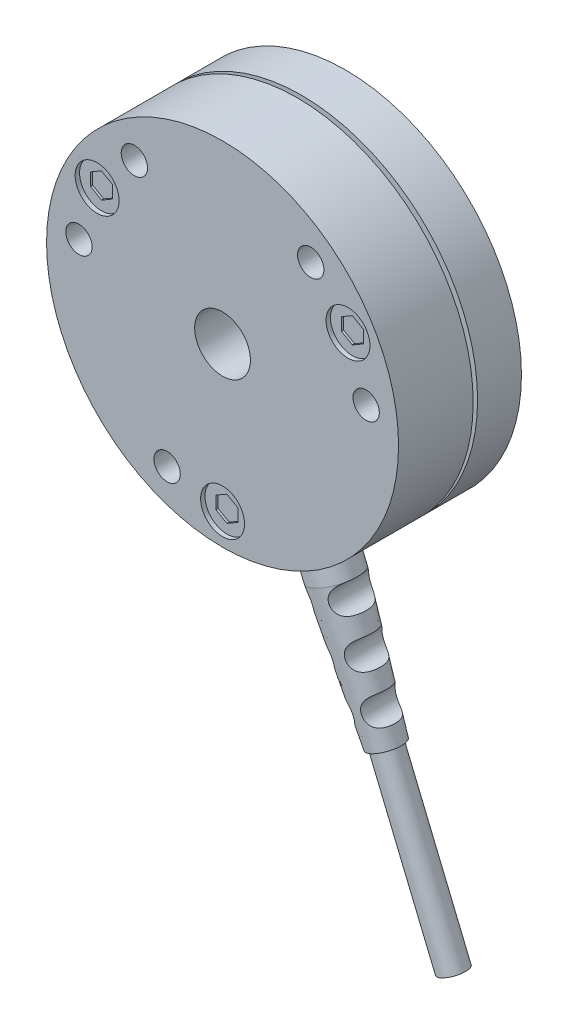
SolidWorks part; units mm, degrees
other "Camera1"
material "Plain Carbon Steel"
ref_plane "Front Plane" through (0, 0, 0) normal (0, 0, 1) x (1, 0, 0)
ref_plane "Top Plane" through (0, 0, 0) normal (0, 1, 0) x (1, 0, 0)
ref_plane "Right Plane" through (0, 0, 0) normal (1, 0, 0) x (0, 0, -1)
sketch "Sketch1" plane through (0, 0, 0) normal (0, 0, 1) x (1, 0, 0)
  circle A0 centre (0, 0) radius 20.05
  dimension "D1" = 40.1
extrude "Boss-Extrude1" add sketch "Sketch1" along normal blind 5
sketch "Sketch2" plane through (0, 0, 5) normal (0, 0, 1) x (1, 0, 0)
  circle A0 centre (0, 0) radius 18.5
  dimension "D1" = 37
extrude "Boss-Extrude2" add sketch "Sketch2" along normal blind 0.5
sketch "Sketch3" plane through (0, 0, 5.5) normal (0, 0, 1) x (1, 0, 0)
  circle A0 centre (0, 0) radius 20.05
extrude "Boss-Extrude3" add sketch "Sketch3" along normal blind 8.5
sketch "Sketch7" plane through (0, 0, 14) normal (0, 0, 1) x (1, 0, 0)
  line L0 (0, 0) -> (7.6728, -18.5238) construction
  line L1 (0, 20.05) -> (0, -20.05) construction
  line L2 (-18.5238, -7.6728) -> (18.5238, 7.6728)
  circle A0 centre (0, 0) radius 20.05 construction
  dimension "D1" = 22.5
sketch "Sketch8" plane through (0, 0, 0) normal (0, 0, -1) x (-1, 0, 0)
  line L0 (-18.5238, 7.6728) -> (18.5238, -7.6728)
  point P3 (0, 0)
ref_plane "Plane4" through (0, 0, 0) normal (-0.3827, 0.9239, 0) x (0.9239, 0.3827, 0)
sketch "Sketch4" plane through (0, 0, 0) normal (-0.3827, 0.9239, 0) x (0.9239, 0.3827, 0)
  line L0 (0, 0) -> (0, -14) construction
  line L1 (-20.05, -14) -> (20.05, -14) construction
  line L2 (-20.05, -7) -> (20.05, -7) construction
  line L3 (-20.05, -5.5) -> (-20.05, -14) construction
  line L4 (20.05, -14) -> (20.05, -5.5) construction
  circle A0 centre (0, -9.65) radius 2.65
  dimension "D1" = 5.3
  dimension "D2" = 7
extrude "Boss-Extrude4" add sketch "Sketch4" against normal blind 37.35 contours A0
chamfer "Chamfer1" distance 15 angle 3 1 edges at (11.8449, -35.521, 9.65)
sketch "Sketch5" plane through (14.2932, -34.5069, 0) normal (0.3827, -0.9239, 0) x (-0.9239, -0.3827, 0)
  circle A0 centre (0, -9.65) radius 1.5
  dimension "D1" = 3
extrude "Boss-Extrude5" add sketch "Sketch5" along normal blind 20
sketch "Sketch6" plane through (0, 0, 0) normal (0, 0, 1) x (1, 0, 0)
  line L0 (11.0013, -19.6346) -> (16.0152, -33.7936) construction
  line L1 (16.0152, -33.7936) -> (18.3361, -40.3477) construction
  line L2 (23.3327, -52.4105) -> (15.679, -33.9329) construction
  line L3 (6.1047, -21.6628) -> (12.5712, -35.2202) construction
  line L4 (12.5712, -35.2202) -> (15.5645, -41.4957) construction
  line L5 (12.9074, -35.0809) -> (20.5611, -53.5585) construction
  line L6 (-921.5262, -418.3454) -> (45272.4504, 18715.8262) construction
  line L7 (-922.1361, -413.1861) -> (45271.8405, 18720.9855) construction
  line L8 (6.1047, -21.6628) -> (11.0013, -19.6346) construction
  circle A0 centre (11.502, -21.0486) radius 1.5
  circle A1 centre (13.1733, -25.7682) radius 1.5
  circle A2 centre (14.8446, -30.4879) radius 1.5
  circle A3 centre (11.0615, -32.0549) radius 1.5
  circle A4 centre (8.906, -27.5358) radius 1.5
  circle A5 centre (6.7505, -23.0167) radius 1.5
  dimension "D1" = 3
  dimension "D2" = 5
  dimension "D3" = 5
extrude "Cut-Extrude1" cut sketch "Sketch6" along normal through all
sketch "Sketch9" plane through (0, 0, 14) normal (0, 0, 1) x (1, 0, 0)
  circle A0 centre (0, 0) radius 16.5 construction
  circle A1 centre (0, -16.5) radius 2.5
  circle A2 centre (-14.2894, 8.25) radius 2.5
  circle A3 centre (14.2894, 8.25) radius 2.5
  dimension "D1" = 33
  dimension "D2" = 5
  dimension "D3" = 3
extrude "Cut-Extrude2" cut sketch "Sketch9" against normal blind 0.5
sketch "Sketch10" plane through (0, 0, 13.5) normal (0, 0, 1) x (1, 0, 0)
  line L0 (-15.5394, 8.9717) -> (-15.5394, 7.5283)
  line L1 (0, -17.9434) -> (1.25, -17.2217)
  line L2 (1.25, -17.2217) -> (1.25, -15.7783)
  line L3 (1.25, -15.7783) -> (0, -15.0566)
  line L4 (0, -15.0566) -> (-1.25, -15.7783)
  line L5 (-1.25, -15.7783) -> (-1.25, -17.2217)
  line L6 (-1.25, -17.2217) -> (0, -17.9434)
  line L7 (-15.5394, 7.5283) -> (-14.2894, 6.8066)
  line L8 (-14.2894, 6.8066) -> (-13.0394, 7.5283)
  line L9 (-13.0394, 7.5283) -> (-13.0394, 8.9717)
  line L10 (-13.0394, 8.9717) -> (-14.2894, 9.6934)
  line L11 (-14.2894, 9.6934) -> (-15.5394, 8.9717)
  line L12 (15.5394, 8.9717) -> (14.2894, 9.6934)
  line L13 (14.2894, 9.6934) -> (13.0394, 8.9717)
  line L14 (13.0394, 8.9717) -> (13.0394, 7.5283)
  line L15 (13.0394, 7.5283) -> (14.2894, 6.8066)
  line L16 (14.2894, 6.8066) -> (15.5394, 7.5283)
  line L17 (15.5394, 7.5283) -> (15.5394, 8.9717)
  circle A0 centre (0, -16.5) radius 1.25 construction
  dimension "D1" = 2.5
  dimension "D2" = 3
extrude "Cut-Extrude3" cut sketch "Sketch10" against normal blind 0.25 contours L1 L2 L3 L4 L5 L6 | L0 L7 L8 L9 L10 L11 | L12 L13 L14 L15 L16 L17
sketch "Sketch11" plane through (0, 0, 14) normal (0, 0, 1) x (1, 0, 0)
  circle A0 centre (0, 0) radius 3.175
  dimension "D1" = 6.35
extrude "Cut-Extrude4" cut sketch "Sketch11" against normal through all contours A0
sketch "Sketch12" plane through (0, 0, 14) normal (0, 0, 1) x (1, 0, 0)
  line L0 (-18.5238, -7.6728) -> (18.5238, 7.6728) construction
  line L1 (0, 0) -> (-7.6728, -18.5238) construction
  line L2 (0, 20.05) -> (0, -20.05) construction
  circle A0 centre (0, 0) radius 16.5 construction
  circle A1 centre (0, 0) radius 20.05 construction
  circle A2 centre (-6.3143, -15.244) radius 1.5
  circle A3 centre (-10.0446, 13.0903) radius 1.5
  circle A4 centre (16.3588, 2.1537) radius 1.5
  point P9 (-6.3143, -15.244)
  dimension "D1" = 33
  dimension "D3" = 3
  dimension "D2" = 22.5
  dimension "D4" = 3
extrude "Cut-Extrude5" cut sketch "Sketch12" against normal blind 5
sketch "Sketch13" plane through (0, 0, 14) normal (0, 0, 1) x (1, 0, 0)
  line L0 (-20.05, 0) -> (20.05, 0) construction
  line L1 (0, 0) -> (-19.8785, 2.6171) construction
  line L2 (0, 0) -> (12.2057, 15.9067) construction
  circle A0 centre (0, 0) radius 20.05 construction
  arc A1 (10.0446, 13.0903) -> (-16.5, 0) centre (0, 0) ccw construction
  circle A2 centre (-16.3588, 2.1537) radius 1.5
  circle A3 centre (10.0446, 13.0903) radius 1.5
  point P11 (-16.3588, 2.1537)
  dimension "D3" = 16.5
  dimension "D4" = 3
  dimension "D5" = 3
  dimension "D1" = 7.5
  dimension "D2" = 120
extrude "Cut-Extrude6" cut sketch "Sketch13" against normal blind 5
sketch "Sketch14" plane through (0, 0, 0) normal (0, 0, -1) x (-1, 0, 0)
  line L0 (0, 0) -> (0, -16.5) construction
  circle A0 centre (0, 0) radius 16.5 construction
  circle A1 centre (0, -16.5) radius 1.5
  circle A2 centre (-14.2894, 8.25) radius 1.5
  circle A3 centre (14.2894, 8.25) radius 1.5
  dimension "D1" = 33
  dimension "D2" = 3
  dimension "D3" = 3
extrude "Cut-Extrude7" cut sketch "Sketch14" against normal blind 5
sketch "Sketch15" plane through (0, 0, 0) normal (0, 0, -1) x (-1, 0, 0)
  line L1 (0, 0) -> (-17.3638, -10.025) construction
  line L2 (18.5238, -7.6728) -> (-18.5238, 7.6728) construction
  line L3 (0, 0) -> (0, 20.05) construction
  circle A1 centre (0, 0) radius 20.05 construction
  circle A2 centre (0, 17.5) radius 1.5
  circle A3 centre (-15.1554, -8.75) radius 1.5
  dimension "D1" = 120
  dimension "D2" = 3
  dimension "D3" = 3
  dimension "D4" = 17.5
  dimension "D5" = 26.25
extrude "Cut-Extrude8" cut sketch "Sketch15" against normal blind 5
sketch "Sketch16" plane through (0, 0, 0) normal (0, 0, -1) x (-1, 0, 0)
  line L0 (0, 20.05) -> (0, -20.05) construction
  circle A0 centre (0, -7.5) radius 3.5
  circle A1 centre (-6.4952, 3.75) radius 3.5
  circle A2 centre (6.4952, 3.75) radius 3.5
  dimension "D1" = 7
  dimension "D2" = 7.5
  dimension "D3" = 3
extrude "Cut-Extrude9" cut sketch "Sketch16" against normal blind 0.5
sketch "Sketch17" plane through (0, 0, 0.5) normal (0, 0, -1) x (-1, 0, 0)
  line L0 (-7.7452, 4.4717) -> (-7.7452, 3.0283)
  line L1 (0, -8.9434) -> (1.25, -8.2217)
  line L2 (1.25, -8.2217) -> (1.25, -6.7783)
  line L3 (1.25, -6.7783) -> (0, -6.0566)
  line L4 (0, -6.0566) -> (-1.25, -6.7783)
  line L5 (-1.25, -6.7783) -> (-1.25, -8.2217)
  line L6 (-1.25, -8.2217) -> (0, -8.9434)
  line L7 (-7.7452, 3.0283) -> (-6.4952, 2.3066)
  line L8 (-6.4952, 2.3066) -> (-5.2452, 3.0283)
  line L9 (-5.2452, 3.0283) -> (-5.2452, 4.4717)
  line L10 (-5.2452, 4.4717) -> (-6.4952, 5.1934)
  line L11 (-6.4952, 5.1934) -> (-7.7452, 4.4717)
  line L12 (7.7452, 4.4717) -> (6.4952, 5.1934)
  line L13 (6.4952, 5.1934) -> (5.2452, 4.4717)
  line L14 (5.2452, 4.4717) -> (5.2452, 3.0283)
  line L15 (5.2452, 3.0283) -> (6.4952, 2.3066)
  line L16 (6.4952, 2.3066) -> (7.7452, 3.0283)
  line L17 (7.7452, 3.0283) -> (7.7452, 4.4717)
  circle A0 centre (0, -7.5) radius 1.25 construction
  dimension "D1" = 2.5
  dimension "D2" = 3
extrude "Cut-Extrude10" cut sketch "Sketch17" against normal blind 0.25 contours L1 L2 L3 L4 L5 L6 | L0 L7 L8 L9 L10 L11 | L12 L13 L14 L15 L16 L17
